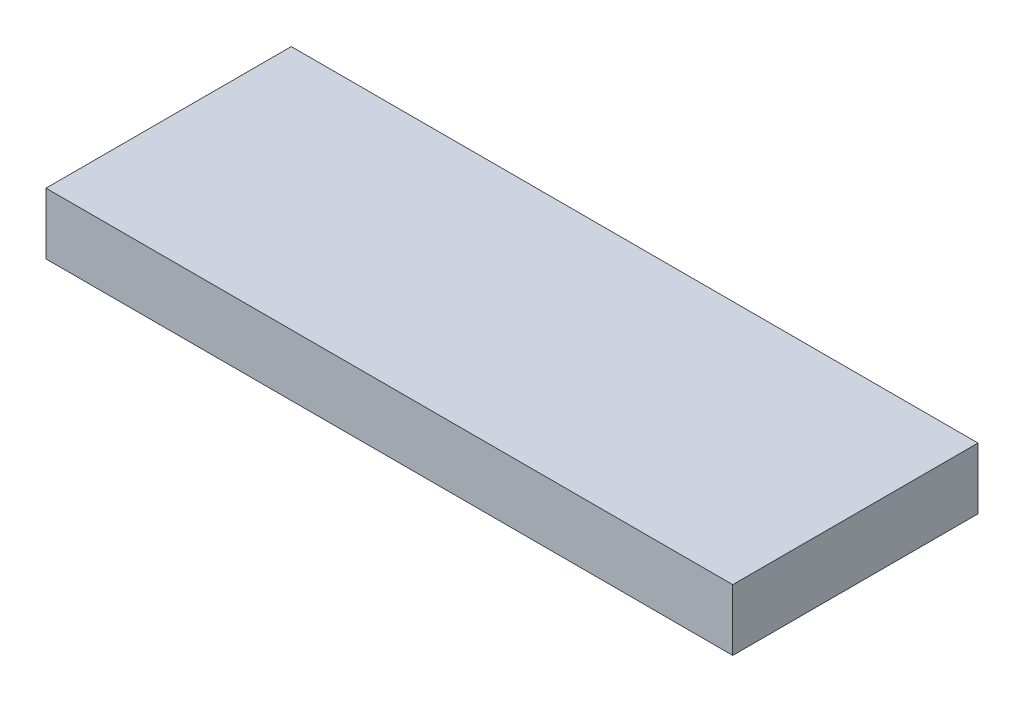
SolidWorks part; units mm, degrees
ref_plane "Front Plane" through (0, 0, 0) normal (0, 0, 1) x (1, 0, 0)
ref_plane "Top Plane" through (0, 0, 0) normal (0, 1, 0) x (1, 0, 0)
ref_plane "Right Plane" through (0, 0, 0) normal (1, 0, 0) x (0, 0, -1)
sketch "Sketch1" plane through (0, 0, 0) normal (0, 1, 0) x (1, 0, 0)
  line L1 (-17.78, 6.35) -> (17.78, 6.35)
  line L2 (-17.78, 6.35) -> (-17.78, -6.35)
  line L3 (-17.78, -6.35) -> (17.78, -6.35)
  line L4 (17.78, 6.35) -> (17.78, -6.35)
  point P4 (0, 6.35)
  point P5 (17.78, 0)
  dimension "D1" = 35.56
  dimension "D2" = 12.7
extrude "Boss-Extrude1" add sketch "Sketch1" along normal blind 3.175
